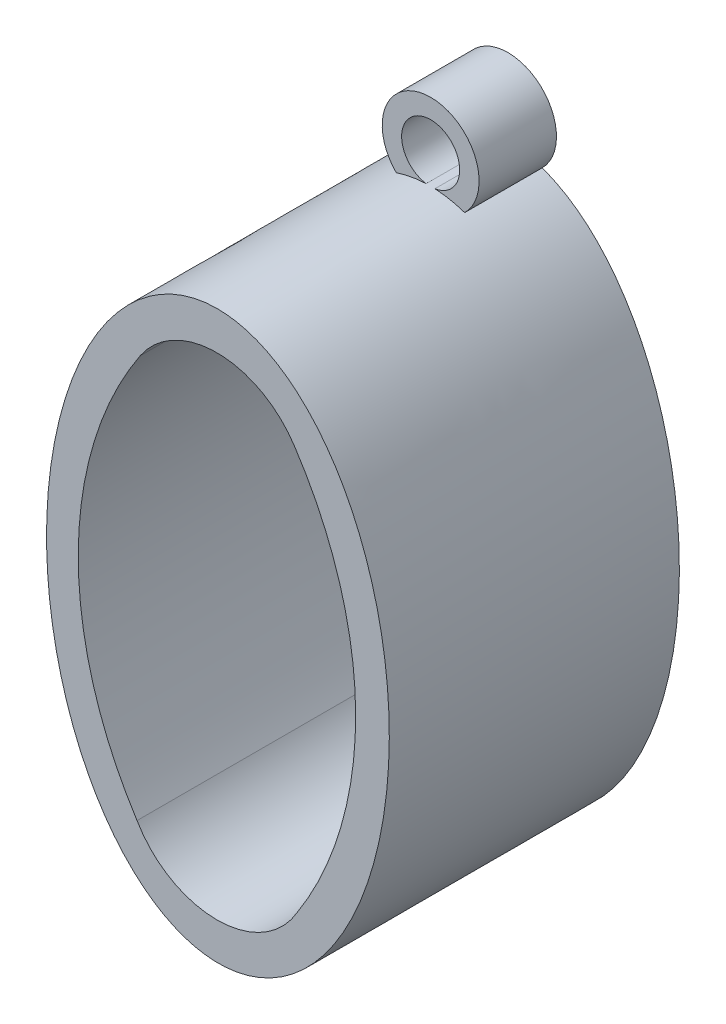
SolidWorks part; units mm, degrees
ref_plane "Plan de face" through (0, 0, 0) normal (0, 0, 1) x (1, 0, 0)
ref_plane "Plan de dessus" through (0, 0, 0) normal (0, 1, 0) x (1, 0, 0)
ref_plane "Plan de droite" through (0, 0, 0) normal (1, 0, 0) x (0, 0, -1)
sketch "Esquisse1" plane through (0, 0, 0) normal (0, 0, 1) x (1, 0, 0)
  line L0 (-0.05, 7.8874) -> (-0.05, -7.9622) construction
  line L1 (11.8274, -0.0308) -> (-11.9278, -0.0308) construction
  arc A0 (3.9595, 10.4809) -> (-4.0232, 10.5362) centre (-0.05, 7.8874) ccw
  arc A1 (-4.1827, -10.3546) -> (4.0862, -10.3484) centre (-0.05, -7.9622) ccw
  arc A2 (4.0862, -10.3484) -> (3.9595, 10.4809) centre (-11.9278, -0.0308) ccw
  arc A3 (-4.0232, 10.5362) -> (-4.1827, -10.3546) centre (11.8274, -0.0308) ccw
  ellipse E0 centre (0, 0) end of major axis (-0.0509, 14.6451) minor radius 8.8622
  point P8 (-0.05, -0.0374)
  point P9 (-0.0502, -0.0308)
  dimension "D1" = 4.7752
  dimension "D2" = 19.05
  dimension "D3" = 25.4
extrude "Boss.-Extru.1" add sketch "Esquisse1" along normal blind 15
sketch "Esquisse2" plane through (0, 0, 0) normal (0, 0, -1) x (-1, 0, 0)
  circle A0 centre (0, 16.1232) radius 2.5046
  circle A1 centre (0, 16.1232) radius 1.5
  dimension "D1" = 5.0092
extrude "Boss.-Extru.2" add sketch "Esquisse2" against normal blind 4
